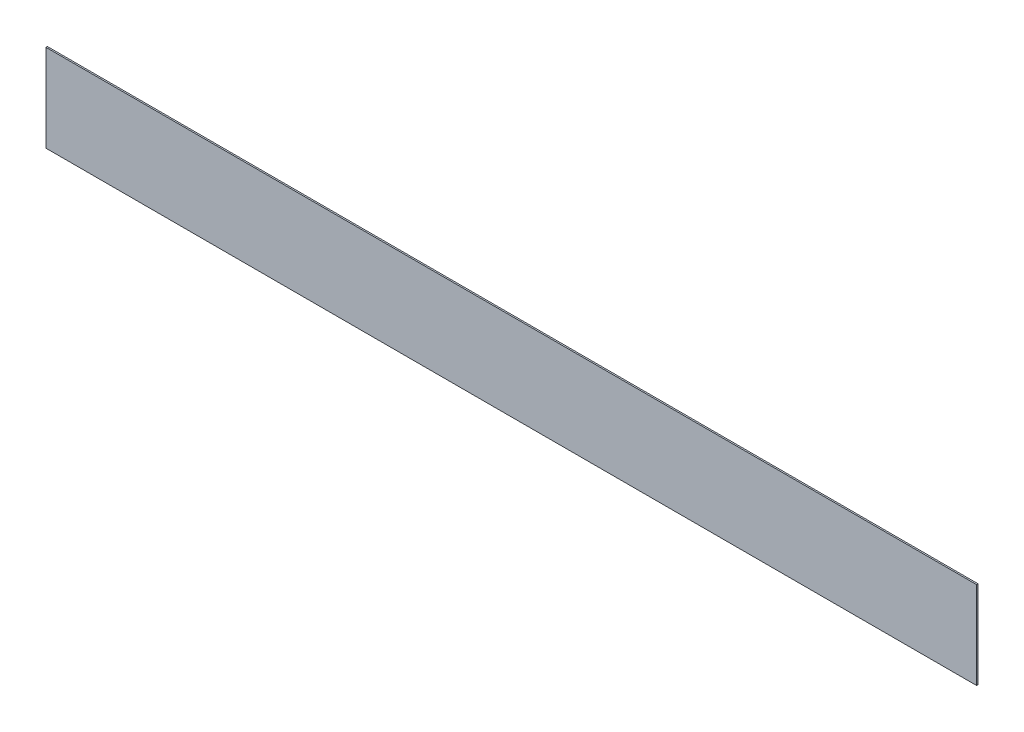
SolidWorks part; units mm, degrees
material "Acier non allié"
ref_plane "Plan de face" through (0, 0, 0) normal (0, 0, 1) x (1, 0, 0)
ref_plane "Plan de dessus" through (0, 0, 0) normal (0, 1, 0) x (1, 0, 0)
ref_plane "Plan de droite" through (0, 0, 0) normal (1, 0, 0) x (0, 0, -1)
sketch "Esquisse1" plane through (0, 0, 0) normal (0, 0, 1) x (1, 0, 0)
  line L1 (0, 0) -> (1278, 0)
  line L2 (0, 0) -> (0, 120)
  line L3 (0, 120) -> (1278, 120)
  line L4 (1278, 0) -> (1278, 120)
  dimension "D1" = 1278
  dimension "D2" = 120
extrude "Boss.-Extru.1" add sketch "Esquisse1" along normal blind 2
